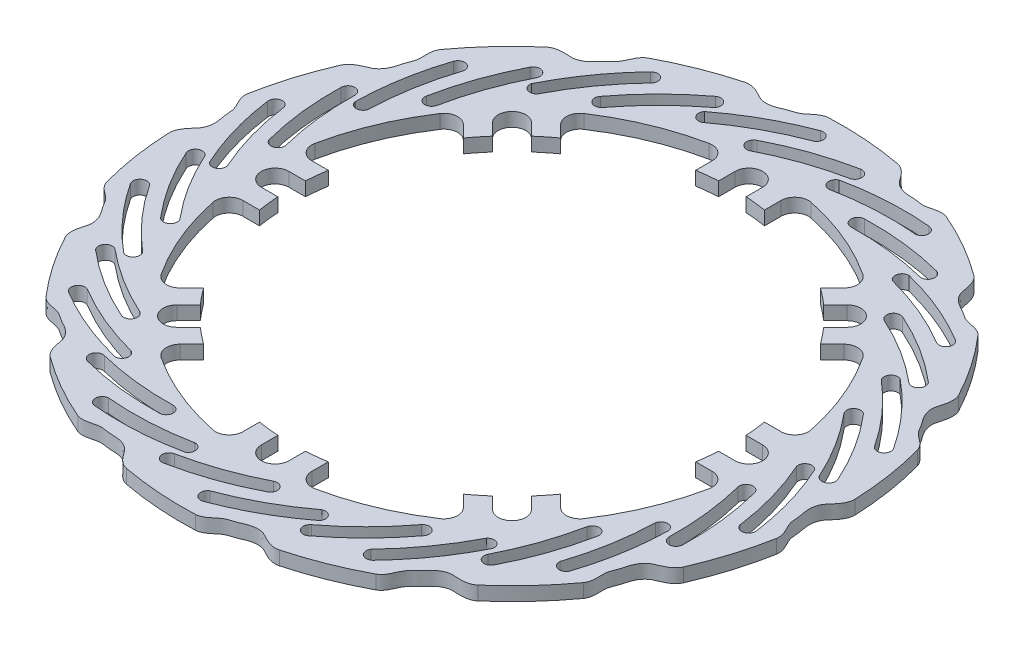
SolidWorks part; units mm, degrees
material "1.0114 (S235J0)"
ref_plane "Płaszczyzna XY" through (0, 0, 0) normal (0, 0, 1) x (1, 0, 0)
ref_plane "Płaszczyzna XZ" through (0, 0, 0) normal (0, 1, 0) x (1, 0, 0)
ref_plane "Płaszczyzna YZ" through (0, 0, 0) normal (1, 0, 0) x (0, 0, -1)
ref_plane "Płaszczyzna1" through (0, 0, 0) normal (0, -1, 0) x (1, 0, 0)
sketch "Szkic1" plane through (0, 0, 0) normal (0, -1, 0) x (1, 0, 0)
  line L0 (-79.2199, 12.5) -> (-85.2218, 12.5)
  line L1 (-69.0997, 51.4221) -> (-64.8558, 47.1781)
  line L2 (-60.1352, 53.0641) -> (-64.3778, 57.3068)
  line L3 (-57.3068, 64.3778) -> (-53.0641, 60.1352)
  line L4 (-47.1781, 64.8558) -> (-51.4221, 69.0997)
  line L5 (-12.5, 85.2218) -> (-12.5, 79.2199)
  line L6 (-5, 80.044) -> (-5, 86.044)
  line L7 (5, 86.044) -> (5, 80.044)
  line L8 (12.5, 79.2199) -> (12.5, 85.2218)
  line L9 (51.4221, 69.0997) -> (47.1781, 64.8558)
  line L10 (53.0641, 60.1352) -> (57.3068, 64.3778)
  line L11 (64.3778, 57.3068) -> (60.1352, 53.0641)
  line L12 (64.8558, 47.1781) -> (69.0997, 51.4221)
  line L13 (85.2218, 12.5) -> (79.2199, 12.5)
  line L14 (80.044, 5) -> (86.044, 5)
  line L15 (86.044, -5) -> (80.044, -5)
  line L16 (79.2199, -12.5) -> (85.2218, -12.5)
  line L17 (69.0997, -51.4221) -> (64.8558, -47.1781)
  line L18 (60.1352, -53.0641) -> (64.3778, -57.3068)
  line L19 (57.3068, -64.3778) -> (53.0641, -60.1352)
  line L20 (47.1781, -64.8558) -> (51.4221, -69.0997)
  line L21 (12.5, -85.2218) -> (12.5, -79.2199)
  line L24 (-12.5, -79.2199) -> (-12.5, -85.2218)
  line L25 (-51.4221, -69.0997) -> (-47.1781, -64.8558)
  line L28 (-64.8558, -47.1781) -> (-69.0997, -51.4221)
  line L29 (-85.2218, -12.5) -> (-79.2199, -12.5)
  line L32 (0, 0) -> (-36.6467, -9.9408) construction
  line L33 (0, 0) -> (-37.3307, 6.9441) construction
  line L34 (-5, -80.044) -> (-5, -86.044)
  line L35 (5, -80.044) -> (5, -86.044)
  line L36 (-57.3068, -64.3778) -> (-53.0641, -60.1352)
  line L37 (-60.1352, -53.0641) -> (-64.3778, -57.3068)
  line L38 (-80.044, 5) -> (-86.044, 5)
  line L39 (-80.044, -5) -> (-86.044, -5)
  arc A0 (2.2683, 114.3343) -> (29.4103, 99.2785) centre (-33.9289, 17.0861) cw
  arc A1 (0.0808, 109.8653) -> (2.2683, 114.3343) centre (1.3962, 111.9913) cw
  arc A2 (29.4103, 99.2785) -> (26.4009, 95.4562) centre (27.4519, 97.7246) cw
  arc A3 (0.0808, 109.8653) -> (26.4009, 95.4562) centre (-36.5073, 11.7894) cw
  arc A4 (-17.0218, 109.5306) -> (10.8424, 99.7654) centre (-37.3307, 6.9441) cw
  arc A5 (-18.0096, 104.6292) -> (-17.0218, 109.5306) centre (-17.5073, 107.0782) cw
  arc A6 (-18.0096, 104.6292) -> (8.6729, 95.2606) centre (-39.0639, 1.9834) cw
  arc A7 (10.8424, 99.7654) -> (8.6729, 95.2606) centre (9.7576, 97.513) cw
  arc A8 (51.6515, 102.0274) -> (69.5731, 76.6862) centre (-23.1555, 30.1153) cw
  arc A9 (47.7416, 98.9502) -> (51.6515, 102.0274) centre (49.8492, 100.2949) cw
  arc A10 (69.5731, 76.6862) -> (65.2033, 74.5481) centre (67.1344, 76.1359) cw
  arc A11 (47.7416, 98.9502) -> (65.2033, 74.5481) centre (-27.7767, 26.4618) cw
  arc A12 (32.1874, 106.0692) -> (53.0552, 85.1812) centre (-30.6209, 22.4536) cw
  arc A13 (29.1708, 102.0817) -> (32.1874, 106.0692) centre (30.6859, 104.0703) cw
  arc A14 (29.1708, 102.0817) -> (49.1461, 82.0638) centre (-34.3348, 18.7362) cw
  arc A15 (53.0552, 85.1812) -> (49.1461, 82.0638) centre (51.1006, 83.6225) cw
  arc A16 (90.8044, 69.5128) -> (95.9561, 38.9053) centre (-7.7958, 37.1797) cw
  arc A17 (85.9466, 68.4367) -> (90.8044, 69.5128) centre (88.4289, 68.7338) cw
  arc A18 (95.9561, 38.9053) -> (91.0914, 38.8749) centre (93.5201, 39.4675) cw
  arc A19 (85.9466, 68.4367) -> (91.0914, 38.8749) centre (-13.5446, 35.8932) cw
  arc A20 (75.0216, 81.5994) -> (84.7599, 53.7258) centre (-17.8462, 33.5159) cw
  arc A21 (70.5736, 79.3157) -> (75.0216, 81.5994) centre (72.8015, 80.4499) cw
  arc A22 (70.5736, 79.3157) -> (79.8852, 52.6132) centre (-22.8053, 31.778) cw
  arc A23 (84.7599, 53.7258) -> (79.8852, 52.6132) centre (82.3225, 53.1695) cw
  arc A24 (111.9724, 23.2303) -> (103.3338, -6.5813) centre (9.1079, 36.8803) cw
  arc A25 (107.1288, 24.3685) -> (111.9724, 23.2303) centre (109.4941, 23.5592) cw
  arc A26 (103.3338, -6.5813) -> (98.9377, -4.498) centre (101.383, -5.0178) cw
  arc A27 (107.1288, 24.3685) -> (98.9377, -4.498) centre (3.3702, 38.2154) cw
  arc A28 (102.9967, 40.9679) -> (99.6768, 11.6294) centre (-1.5369, 37.94) cw
  arc A29 (97.9984, 40.8403) -> (102.9967, 40.9679) centre (100.4978, 40.8955) cw
  arc A30 (97.9984, 40.8403) -> (94.8021, 12.742) centre (-6.7589, 38.5259) cw
  arc A31 (99.6768, 11.6294) -> (94.8021, 12.742) centre (97.2394, 12.1857) cw
  arc A32 (110.9629, -27.6532) -> (90.245, -50.7644) centre (24.2077, 29.2762) cw
  arc A33 (107.0928, -24.5261) -> (110.9629, -27.6532) centre (108.8728, -26.2816) cw
  arc A34 (90.245, -50.7644) -> (87.1882, -46.98) centre (89.1658, -48.5094) cw
  arc A35 (107.0928, -24.5261) -> (87.1882, -46.98) centre (19.6175, 32.9686) cw
  arc A36 (110.5722, -7.7778) -> (94.8515, -32.7704) centre (15.0769, 34.8495) cw
  arc A37 (106.0135, -5.7241) -> (110.5722, -7.7778) centre (108.2893, -6.7588) cw
  arc A38 (106.0135, -5.7241) -> (90.9423, -29.653) centre (10.6262, 37.6432) cw
  arc A39 (94.8515, -32.7704) -> (90.9423, -29.653) centre (92.8969, -31.2117) cw
  arc A40 (87.9759, -73.0597) -> (59.2821, -84.893) centre (34.5128, 15.8736) cw
  arc A41 (85.8458, -68.5631) -> (87.9759, -73.0597) centre (86.6878, -70.917) cw
  arc A42 (59.2821, -84.893) -> (58.17, -80.157) centre (59.2882, -82.393) cw
  arc A43 (85.8458, -68.5631) -> (58.17, -80.157) centre (31.9793, 21.192) cw
  arc A44 (96.2474, -54.983) -> (71.2397, -70.6796) centre (28.7044, 24.8567) cw
  arc A45 (93.0312, -51.1547) -> (96.2474, -54.983) centre (94.6328, -53.0744) cw
  arc A46 (93.0312, -51.1547) -> (69.0702, -66.1748) centre (25.9066, 29.3048) cw
  arc A47 (71.2397, -70.6796) -> (69.0702, -66.1748) centre (70.155, -68.4272) cw
  arc A48 (47.5641, -103.9958) -> (16.5776, -102.2075) centre (37.9823, -0.6729) cw
  arc A49 (47.5959, -99.0203) -> (47.5641, -103.9958) centre (47.3332, -101.5065) cw
  arc A50 (16.5776, -102.2075) -> (17.6305, -97.458) centre (17.6678, -99.9577) cw
  arc A51 (47.5959, -99.0203) -> (17.6305, -97.458) centre (38.0072, 5.2181) cw
  arc A52 (62.8597, -91.2982) -> (33.518, -94.5899) centre (36.6467, 9.9408) cw
  arc A53 (61.623, -86.4536) -> (62.8597, -91.2982) centre (62.233, -88.878) cw
  arc A54 (61.623, -86.4536) -> (33.518, -89.5899) centre (36.0559, 15.1622) cw
  arc A55 (33.518, -94.5899) -> (33.518, -89.5899) centre (33.518, -92.0899) cw
  arc A56 (-2.2683, -114.3343) -> (-29.4103, -99.2785) centre (33.9289, -17.0861) cw
  arc A57 (-0.0808, -109.8653) -> (-2.2683, -114.3343) centre (-1.3962, -111.9913) cw
  arc A58 (-29.4103, -99.2785) -> (-26.4009, -95.4562) centre (-27.4519, -97.7246) cw
  arc A59 (-0.0808, -109.8653) -> (-26.4009, -95.4562) centre (36.5073, -11.7894) cw
  arc A60 (17.0218, -109.5306) -> (-10.8424, -99.7654) centre (37.3307, -6.9441) cw
  arc A61 (18.0096, -104.6292) -> (17.0218, -109.5306) centre (17.5073, -107.0782) cw
  arc A62 (18.0096, -104.6292) -> (-8.6729, -95.2606) centre (39.0639, -1.9834) cw
  arc A63 (-10.8424, -99.7654) -> (-8.6729, -95.2606) centre (-9.7576, -97.513) cw
  arc A64 (-51.6515, -102.0274) -> (-69.5731, -76.6862) centre (23.1555, -30.1153) cw
  arc A65 (-47.7416, -98.9502) -> (-51.6515, -102.0274) centre (-49.8492, -100.2949) cw
  arc A66 (-69.5731, -76.6862) -> (-65.2033, -74.5481) centre (-67.1344, -76.1359) cw
  arc A67 (-47.7416, -98.9502) -> (-65.2033, -74.5481) centre (27.7767, -26.4618) cw
  arc A68 (-32.1874, -106.0692) -> (-53.0552, -85.1812) centre (30.6209, -22.4536) cw
  arc A69 (-29.1708, -102.0817) -> (-32.1874, -106.0692) centre (-30.6859, -104.0703) cw
  arc A70 (-29.1708, -102.0817) -> (-49.1461, -82.0638) centre (34.3348, -18.7362) cw
  arc A71 (-53.0552, -85.1812) -> (-49.1461, -82.0638) centre (-51.1006, -83.6225) cw
  arc A72 (-90.8044, -69.5128) -> (-95.9561, -38.9053) centre (7.7958, -37.1797) cw
  arc A73 (-85.9466, -68.4367) -> (-90.8044, -69.5128) centre (-88.4289, -68.7338) cw
  arc A74 (-95.9561, -38.9053) -> (-91.0914, -38.8749) centre (-93.5201, -39.4675) cw
  arc A75 (-85.9466, -68.4367) -> (-91.0914, -38.8749) centre (13.5446, -35.8932) cw
  arc A76 (-75.0216, -81.5994) -> (-84.7599, -53.7258) centre (17.8462, -33.5159) cw
  arc A77 (-70.5736, -79.3157) -> (-75.0216, -81.5994) centre (-72.8015, -80.4499) cw
  arc A78 (-70.5736, -79.3157) -> (-79.8852, -52.6132) centre (22.8053, -31.778) cw
  arc A79 (-84.7599, -53.7258) -> (-79.8852, -52.6132) centre (-82.3225, -53.1695) cw
  arc A80 (-111.9724, -23.2303) -> (-103.3338, 6.5813) centre (-9.1079, -36.8803) cw
  arc A81 (-107.1288, -24.3685) -> (-111.9724, -23.2303) centre (-109.4941, -23.5592) cw
  arc A82 (-103.3338, 6.5813) -> (-98.9377, 4.498) centre (-101.383, 5.0178) cw
  arc A83 (-107.1288, -24.3685) -> (-98.9377, 4.498) centre (-3.3702, -38.2154) cw
  arc A84 (-102.9967, -40.9679) -> (-99.6768, -11.6294) centre (1.5369, -37.94) cw
  arc A85 (-97.9984, -40.8403) -> (-102.9967, -40.9679) centre (-100.4978, -40.8955) cw
  arc A86 (-97.9984, -40.8403) -> (-94.8021, -12.742) centre (6.7589, -38.5259) cw
  arc A87 (-99.6768, -11.6294) -> (-94.8021, -12.742) centre (-97.2394, -12.1857) cw
  arc A88 (-110.9629, 27.6532) -> (-90.245, 50.7644) centre (-24.2077, -29.2762) cw
  arc A89 (-107.0928, 24.5261) -> (-110.9629, 27.6532) centre (-108.8728, 26.2816) cw
  arc A90 (-90.245, 50.7644) -> (-87.1882, 46.98) centre (-89.1658, 48.5094) cw
  arc A91 (-107.0928, 24.5261) -> (-87.1882, 46.98) centre (-19.6175, -32.9686) cw
  arc A92 (-110.5722, 7.7778) -> (-94.8515, 32.7704) centre (-15.0769, -34.8495) cw
  arc A93 (-106.0135, 5.7241) -> (-110.5722, 7.7778) centre (-108.2893, 6.7588) cw
  arc A94 (-106.0135, 5.7241) -> (-90.9423, 29.653) centre (-10.6262, -37.6432) cw
  arc A95 (-94.8515, 32.7704) -> (-90.9423, 29.653) centre (-92.8969, 31.2117) cw
  arc A98 (-61.623, 86.4536) -> (-62.8597, 91.2982) centre (-62.233, 88.878) cw
  arc A99 (-87.9759, 73.0597) -> (-59.2821, 84.893) centre (-34.5128, -15.8736) cw
  arc A100 (-85.8458, 68.5631) -> (-87.9759, 73.0597) centre (-86.6878, 70.917) cw
  arc A101 (-33.518, 94.5899) -> (-33.518, 89.5899) centre (-33.518, 92.0899) cw
  arc A103 (-47.5959, 99.0203) -> (-47.5641, 103.9958) centre (-47.3332, 101.5065) cw
  arc A104 (-47.5959, 99.0203) -> (-17.6305, 97.458) centre (-38.0072, -5.2181) cw
  arc A106 (-16.5776, 102.2075) -> (-17.6305, 97.458) centre (-17.6678, 99.9577) cw
  arc A110 (-47.5641, 103.9958) -> (-16.5776, 102.2075) centre (-37.9823, 0.6729) cw
  arc A114 (-61.623, 86.4536) -> (-33.518, 89.5899) centre (-36.0559, -15.1622) cw
  arc A115 (-62.8597, 91.2982) -> (-33.518, 94.5899) centre (-36.6467, -9.9408) cw
  arc A116 (-59.2821, 84.893) -> (-58.17, 80.157) centre (-59.2882, 82.393) cw
  arc A117 (-85.8458, 68.5631) -> (-58.17, 80.157) centre (-31.9793, -21.192) cw
  arc A118 (-96.2474, 54.983) -> (-71.2397, 70.6796) centre (-28.7044, -24.8567) cw
  arc A119 (-93.0312, 51.1547) -> (-96.2474, 54.983) centre (-94.6328, 53.0744) cw
  arc A120 (-93.0312, 51.1547) -> (-69.0702, 66.1748) centre (-25.9066, -29.3048) cw
  arc A121 (-71.2397, 70.6796) -> (-69.0702, 66.1748) centre (-70.155, 68.4272) cw
  arc A122 (31.3153, 115.8419) -> (56.4795, 105.8776) centre (0, 0) cw
  arc A123 (78.4761, 90.7827) -> (96.8248, 70.8869) centre (0, 0) cw
  arc A124 (110.0936, 47.7429) -> (117.9928, 21.8562) centre (0, 0) cw
  arc A125 (119.9058, -4.7529) -> (115.7909, -31.5034) centre (0, 0) cw
  arc A126 (105.9692, -56.3074) -> (90.6552, -78.6234) centre (0, 0) cw
  arc A127 (71.0441, -96.7096) -> (47.5641, -110.171) centre (0, 0) cw
  arc A128 (22.0478, -117.9572) -> (-4.9477, -119.898) centre (0, 0) cw
  arc A129 (-31.3153, -115.8419) -> (-56.4795, -105.8776) centre (0, 0) cw
  arc A130 (-78.4761, -90.7827) -> (-96.8248, -70.8869) centre (0, 0) cw
  arc A131 (-110.0936, -47.7429) -> (-117.9928, -21.8562) centre (0, 0) cw
  arc A132 (-119.9058, 4.7529) -> (-115.7909, 31.5034) centre (0, 0) cw
  arc A133 (-105.9692, 56.3074) -> (-90.6552, 78.6234) centre (0, 0) cw
  arc A134 (-71.0441, 96.7096) -> (-47.5641, 110.171) centre (0, 0) cw
  arc A135 (-12.5, -79.2199) -> (-5, -80.044) centre (0, 0) ccw
  arc A136 (-53.0641, -60.1352) -> (-47.1781, -64.8558) centre (0, 0) ccw
  arc A137 (-64.8558, -47.1781) -> (-60.1352, -53.0641) centre (0, 0) ccw
  arc A138 (-80.044, -5) -> (-79.2199, -12.5) centre (0, 0) ccw
  arc A139 (-79.2199, 12.5) -> (-80.044, 5) centre (0, 0) ccw
  arc A140 (-60.1352, 53.0641) -> (-64.8558, 47.1781) centre (0, 0) ccw
  arc A141 (-47.1781, 64.8558) -> (-53.0641, 60.1352) centre (0, 0) ccw
  arc A142 (-5, 80.044) -> (-12.5, 79.2199) centre (0, 0) ccw
  arc A143 (64.8558, 47.1781) -> (60.1352, 53.0641) centre (0, 0) ccw
  arc A144 (-85.2218, 12.5) -> (-90.1196, 18.5057) centre (-85.2218, 17.5) cw
  arc A145 (-90.1196, 18.5057) -> (-76.8097, 50.6386) centre (0, 0) cw
  arc A146 (-76.8097, 50.6386) -> (-69.0997, 51.4221) centre (-72.6353, 47.8865) cw
  arc A148 (-64.3778, 57.3068) -> (-57.3068, 64.3778) centre (-60.8423, 60.8423) cw
  arc A150 (-51.4221, 69.0997) -> (-50.6386, 76.8097) centre (-47.8865, 72.6353) cw
  arc A151 (-50.6386, 76.8097) -> (-18.5057, 90.1196) centre (0, 0) cw
  arc A152 (-18.5057, 90.1196) -> (-12.5, 85.2218) centre (-17.5, 85.2218) cw
  arc A154 (-5, 86.044) -> (5, 86.044) centre (0, 86.044) cw
  arc A156 (12.5, 85.2218) -> (18.5057, 90.1196) centre (17.5, 85.2218) cw
  arc A157 (18.5057, 90.1196) -> (50.6386, 76.8097) centre (0, 0) cw
  arc A158 (50.6386, 76.8097) -> (51.4221, 69.0997) centre (47.8865, 72.6353) cw
  arc A160 (57.3068, 64.3778) -> (64.3778, 57.3068) centre (60.8423, 60.8423) cw
  arc A162 (69.0997, 51.4221) -> (76.8097, 50.6386) centre (72.6353, 47.8865) cw
  arc A163 (76.8097, 50.6386) -> (90.1196, 18.5057) centre (0, 0) cw
  arc A164 (90.1196, 18.5057) -> (85.2218, 12.5) centre (85.2218, 17.5) cw
  arc A166 (86.044, 5) -> (86.044, -5) centre (86.044, 0) cw
  arc A168 (85.2218, -12.5) -> (90.1196, -18.5057) centre (85.2218, -17.5) cw
  arc A169 (90.1196, -18.5057) -> (76.8097, -50.6386) centre (0, 0) cw
  arc A170 (76.8097, -50.6386) -> (69.0997, -51.4221) centre (72.6353, -47.8865) cw
  arc A172 (64.3778, -57.3068) -> (57.3068, -64.3778) centre (60.8423, -60.8423) cw
  arc A174 (51.4221, -69.0997) -> (50.6386, -76.8097) centre (47.8865, -72.6353) cw
  arc A175 (50.6386, -76.8097) -> (18.5057, -90.1196) centre (0, 0) cw
  arc A176 (18.5057, -90.1196) -> (12.5, -85.2218) centre (17.5, -85.2218) cw
  arc A180 (-12.5, -85.2218) -> (-18.5057, -90.1196) centre (-17.5, -85.2218) cw
  arc A181 (-18.5057, -90.1196) -> (-50.6386, -76.8097) centre (0, 0) cw
  arc A182 (-50.6386, -76.8097) -> (-51.4221, -69.0997) centre (-47.8865, -72.6353) cw
  arc A186 (-69.0997, -51.4221) -> (-76.8097, -50.6386) centre (-72.6353, -47.8865) cw
  arc A187 (-76.8097, -50.6386) -> (-90.1196, -18.5057) centre (0, 0) cw
  arc A188 (-90.1196, -18.5057) -> (-85.2218, -12.5) centre (-85.2218, -17.5) cw
  arc A192 (-22.0478, 117.9572) -> (4.9477, 119.898) centre (0, 0) cw
  arc A193 (80.044, 5) -> (79.2199, 12.5) centre (0, 0) ccw
  arc A194 (79.2199, -12.5) -> (80.044, -5) centre (0, 0) ccw
  arc A195 (60.1352, -53.0641) -> (64.8558, -47.1781) centre (0, 0) ccw
  arc A196 (47.1781, -64.8558) -> (53.0641, -60.1352) centre (0, 0) ccw
  arc A197 (5, -80.044) -> (12.5, -79.2199) centre (0, 0) ccw
  arc A198 (12.5, 79.2199) -> (5, 80.044) centre (0, 0) ccw
  arc A199 (53.0641, 60.1352) -> (47.1781, 64.8558) centre (0, 0) ccw
  arc A200 (5, -86.044) -> (-5, -86.044) centre (0, -86.044) cw
  arc A201 (-57.3068, -64.3778) -> (-64.3778, -57.3068) centre (-60.8423, -60.8423) cw
  arc A202 (-86.044, 5) -> (-86.044, -5) centre (-86.044, 0) ccw
  spline S0 degree 3 poles (-47.5641, 110.171) (-46.1183, 110.7037) (-43.5046, 110.4098) (-39.951, 109.2236) (-36.3996, 110.0749) (-32.6442, 109.8724) (-28.547, 111.506) (-26.2979, 115.4353) (-23.7939, 117.6336) (-22.0478, 117.9572) knots 0 0 0 0 0.147554 0.283238 0.382647 0.52482 0.681961 0.812366 1 1 1 1
  spline S1 degree 3 poles (4.9477, 119.898) (6.4814, 119.7506) (8.7087, 118.3518) (11.3957, 115.7412) (14.9648, 114.9673) (18.2605, 113.1554) (22.6607, 112.8495) (26.3919, 115.4138) (29.6017, 116.308) (31.3153, 115.8419) knots 0 0 0 0 0.147554 0.283238 0.382647 0.52482 0.681961 0.812366 1 1 1 1
  spline S2 degree 3 poles (56.4795, 105.8776) (57.7974, 105.0794) (59.1972, 102.8527) (60.4854, 99.3348) (63.3652, 97.0889) (65.5484, 94.0266) (69.3801, 91.8418) (73.8544, 92.5333) (77.1344, 91.9462) (78.4761, 90.7827) knots 0 0 0 0 0.147554 0.283238 0.382647 0.52482 0.681961 0.812366 1 1 1 1
  spline S3 degree 3 poles (96.8248, 70.8869) (97.6658, 69.5959) (97.9609, 66.9824) (97.5952, 63.2539) (99.2154, 59.981) (99.8537, 56.2746) (102.358, 52.6437) (106.6892, 51.3254) (109.3897, 49.3733) (110.0936, 47.7429) knots 0 0 0 0 0.147554 0.283238 0.382647 0.52482 0.681961 0.812366 1 1 1 1
  spline S4 degree 3 poles (117.9928, 21.8562) (118.1904, 20.3281) (117.3223, 17.8454) (115.3751, 14.6448) (115.4148, 10.993) (114.3817, 7.3768) (115.0626, 3.0189) (118.3929, -0.0482) (119.979, -2.9786) (119.9058, -4.7529) knots 0 0 0 0 0.147554 0.283238 0.382647 0.52482 0.681961 0.812366 1 1 1 1
  spline S5 degree 3 poles (115.7909, -31.5034) (115.3059, -32.9659) (113.4466, -34.8261) (110.3035, -36.8648) (108.7548, -40.1722) (106.255, -42.9821) (104.9777, -47.2039) (106.6474, -51.4122) (106.805, -54.7405) (105.9692, -56.3074) knots 0 0 0 0 0.147554 0.283238 0.382647 0.52482 0.681961 0.812366 1 1 1 1
  spline S6 degree 3 poles (90.6552, -78.6234) (89.5837, -79.7306) (87.1013, -80.5999) (83.385, -81.073) (80.5546, -83.3809) (77.0832, -84.8278) (74.1006, -88.0774) (73.7791, -92.5933) (72.4769, -95.6604) (71.0441, -96.7096) knots 0 0 0 0 0.147554 0.283238 0.382647 0.52482 0.681961 0.812366 1 1 1 1
  spline S7 degree 3 poles (47.5641, -110.171) (46.1183, -110.7037) (43.5046, -110.4098) (39.951, -109.2236) (36.3996, -110.0749) (32.6442, -109.8724) (28.547, -111.506) (26.2979, -115.4353) (23.7939, -117.6336) (22.0478, -117.9572) knots 0 0 0 0 0.147554 0.283238 0.382647 0.52482 0.681961 0.812366 1 1 1 1
  spline S8 degree 3 poles (-4.9477, -119.898) (-6.4814, -119.7506) (-8.7087, -118.3518) (-11.3957, -115.7412) (-14.9648, -114.9673) (-18.2605, -113.1554) (-22.6607, -112.8495) (-26.3919, -115.4138) (-29.6017, -116.308) (-31.3153, -115.8419) knots 0 0 0 0 0.147554 0.283238 0.382647 0.52482 0.681961 0.812366 1 1 1 1
  spline S9 degree 3 poles (-56.4795, -105.8776) (-57.7974, -105.0794) (-59.1972, -102.8527) (-60.4854, -99.3348) (-63.3652, -97.0889) (-65.5484, -94.0266) (-69.3801, -91.8418) (-73.8544, -92.5333) (-77.1344, -91.9462) (-78.4761, -90.7827) knots 0 0 0 0 0.147554 0.283238 0.382647 0.52482 0.681961 0.812366 1 1 1 1
  spline S10 degree 3 poles (-96.8248, -70.8869) (-97.6658, -69.5959) (-97.9609, -66.9824) (-97.5952, -63.2539) (-99.2154, -59.981) (-99.8537, -56.2746) (-102.358, -52.6437) (-106.6892, -51.3254) (-109.3897, -49.3733) (-110.0936, -47.7429) knots 0 0 0 0 0.147554 0.283238 0.382647 0.52482 0.681961 0.812366 1 1 1 1
  spline S11 degree 3 poles (-117.9928, -21.8562) (-118.1904, -20.3281) (-117.3223, -17.8454) (-115.3751, -14.6448) (-115.4148, -10.993) (-114.3817, -7.3768) (-115.0626, -3.0189) (-118.3929, 0.0482) (-119.979, 2.9786) (-119.9058, 4.7529) knots 0 0 0 0 0.147554 0.283238 0.382647 0.52482 0.681961 0.812366 1 1 1 1
  spline S12 degree 3 poles (-115.7909, 31.5034) (-115.3059, 32.9659) (-113.4466, 34.8261) (-110.3035, 36.8648) (-108.7548, 40.1722) (-106.255, 42.9821) (-104.9777, 47.2039) (-106.6474, 51.4122) (-106.805, 54.7405) (-105.9692, 56.3074) knots 0 0 0 0 0.147554 0.283238 0.382647 0.52482 0.681961 0.812366 1 1 1 1
  spline S13 degree 3 poles (-90.6552, 78.6234) (-89.5837, 79.7306) (-87.1013, 80.5999) (-83.385, 81.073) (-80.5546, 83.3809) (-77.0832, 84.8278) (-74.1006, 88.0774) (-73.7791, 92.5933) (-72.4769, 95.6604) (-71.0441, 96.7096) knots 0 0 0 0 0.147554 0.283238 0.382647 0.52482 0.681961 0.812366 1 1 1 1
  point P475 (0, 0)
  dimension "D1" = 14
  dimension "D3" = 160.4
  dimension "D6" = 6.0019
  dimension "D2" = 25.714
  dimension "D4" = 6
  dimension "D5" = 6
  dimension "D7" = 6
  dimension "D8" = 6
  dimension "D9" = 6
  dimension "D10" = 6
  dimension "D11" = 6
  dimension "D12" = 6
  dimension "D13" = 6
  dimension "D14" = 6
extrude "Dodanie-wyciągnięcie1" add sketch "Szkic1" against normal blind 5
